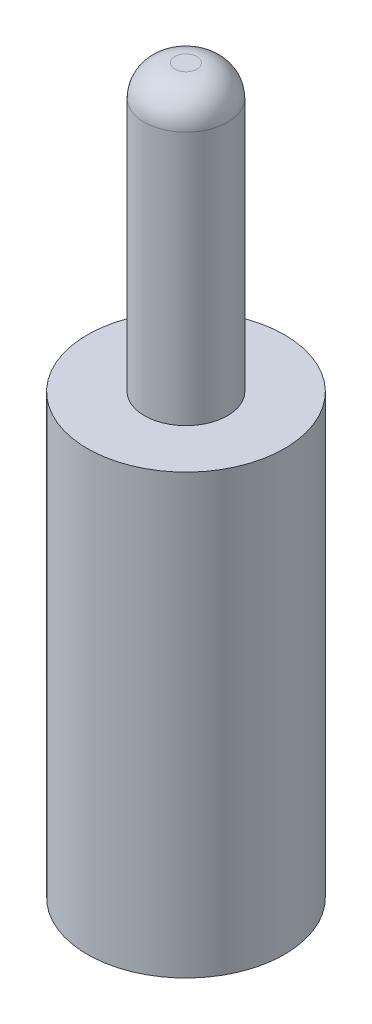
SolidWorks part; units mm, degrees
ref_plane "Front" through (0, 0, 0) normal (0, 0, 1) x (1, 0, 0)
ref_plane "Top" through (0, 0, 0) normal (0, 1, 0) x (1, 0, 0)
ref_plane "Right" through (0, 0, 0) normal (1, 0, 0) x (0, 0, -1)
sketch "Sketch1" plane through (0, 0, 0) normal (0, 1, 0) x (1, 0, 0)
  circle A0 centre (0, 0) radius 0.95
  circle A1 centre (0, 0) radius 2.1
  dimension "D1" = 1.9
  dimension "D2" = 4.2
extrude "Boss-Extrude1" add sketch "Sketch1" along normal blind 6.5 contours A0
sketch "Sketch2" plane through (0, 0, 0) normal (0, -1, 0) x (-1, 0, 0)
  circle A0 centre (0, 0) radius 2.25
  dimension "D1" = 4.5
extrude "Boss-Extrude2" add sketch "Sketch2" along normal blind 10
fillet "Fillet1" radius 0.7 1 edges at (0, 6.5, 0.95)
